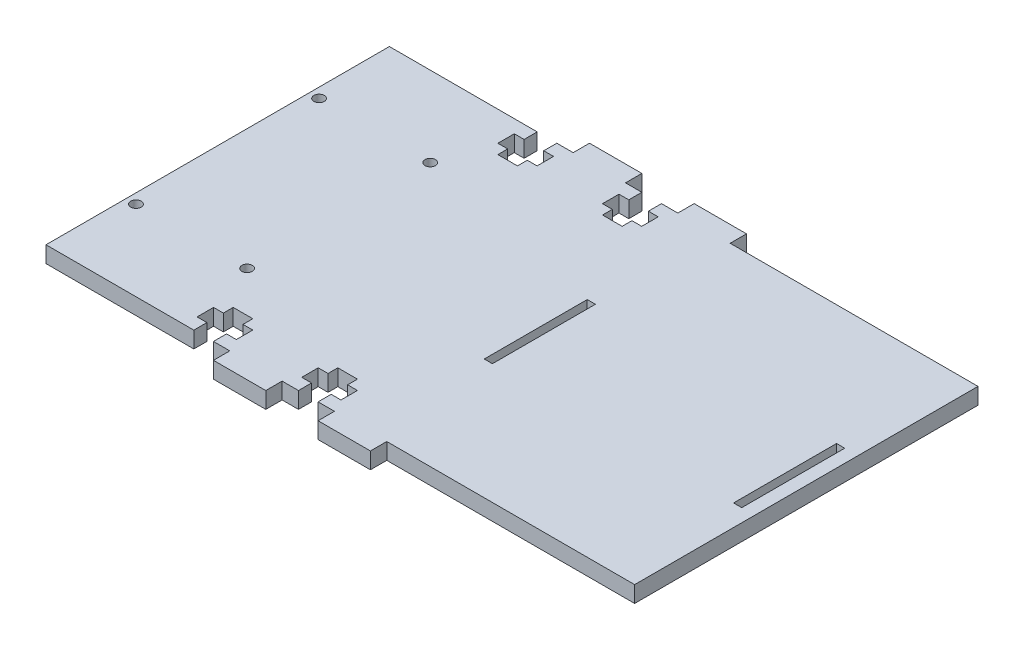
SolidWorks part; units mm, degrees
ref_plane "Front Plane" through (0, 0, 0) normal (0, 0, 1) x (1, 0, 0)
ref_plane "Top Plane" through (0, 0, 0) normal (0, 1, 0) x (1, 0, 0)
ref_plane "Right Plane" through (0, 0, 0) normal (1, 0, 0) x (0, 0, -1)
sketch "Sketch1" plane through (0, 0, 0) normal (0, 1, 0) x (1, 0, 0)
  line L1 (0, 0) -> (114.3, 0)
  line L2 (0, 0) -> (0, 66.675)
  line L3 (0, 66.675) -> (114.3, 66.675)
  line L4 (114.3, 0) -> (114.3, 66.675)
  line L8 (111.76, 43.3375) -> (110.1725, 43.3375)
  line L9 (111.76, 23.3375) -> (111.76, 43.3375)
  line L10 (110.1725, 23.3375) -> (111.76, 23.3375)
  line L11 (110.1725, 43.3375) -> (110.1725, 23.3375)
  line L12 (111.76, 43.3375) -> (110.1725, 43.3375)
  line L13 (111.76, 23.3375) -> (111.76, 43.3375)
  line L14 (110.1725, 23.3375) -> (111.76, 23.3375)
  line L15 (110.1725, 43.3375) -> (110.1725, 23.3375)
  line L16 (61.7601, 43.3375) -> (61.7601, 23.3375)
  line L17 (63.3476, 43.3375) -> (61.7601, 43.3375)
  line L18 (63.3476, 23.3375) -> (63.3476, 43.3375)
  line L19 (61.7601, 23.3375) -> (63.3476, 23.3375)
  line L20 (61.7601, 43.3375) -> (61.7601, 23.3375)
  line L21 (63.3476, 43.3375) -> (61.7601, 43.3375)
  line L22 (63.3476, 23.3375) -> (63.3476, 43.3375)
  line L23 (61.7601, 23.3375) -> (63.3476, 23.3375)
  circle A0 centre (1.905, 15.5575) radius 1.016 construction
  circle A1 centre (1.905, 15.5575) radius 1.016
  circle A2 centre (23.495, 15.5575) radius 1.016 construction
  circle A3 centre (23.495, 15.5575) radius 1.016
  circle A4 centre (23.495, 51.1175) radius 1.016 construction
  circle A5 centre (23.495, 51.1175) radius 1.016
  circle A6 centre (1.905, 51.1175) radius 1.016 construction
  circle A7 centre (1.905, 51.1175) radius 1.016
  dimension "D1" = 114.3
  dimension "D2" = 66.675
  dimension "D3" = 0
  dimension "D4" = 0
extrude "Boss-Extrude1" add sketch "Sketch1" along normal blind 3.175
sketch "Sketch2" plane through (0, 0, 0) normal (0, 0, 1) x (1, 0, 0)
  line L0 (0, 0) -> (114.3, 0) construction
  line L1 (0, 0) -> (114.3, 0) construction
  line L2 (0, 3.175) -> (114.3, 3.175) construction
  line L3 (0, 3.175) -> (114.3, 3.175) construction
  line L5 (20.4506, 0) -> (25.5306, 0)
  line L6 (20.4506, 0) -> (20.4506, 3.175)
  line L7 (20.4506, 3.175) -> (25.5306, 3.175)
  line L8 (25.5306, 0) -> (25.5306, 3.175)
  line L9 (25.5306, 0) -> (35.6906, 0)
  line L10 (25.5306, 0) -> (25.5306, 3.175)
  line L11 (25.5306, 3.175) -> (35.6906, 3.175)
  line L12 (35.6906, 0) -> (35.6906, 3.175)
  line L13 (35.6906, 0) -> (45.8506, 0)
  line L14 (35.6906, 0) -> (35.6906, 3.175)
  line L15 (35.6906, 3.175) -> (45.8506, 3.175)
  line L16 (45.8506, 0) -> (45.8506, 3.175)
  line L17 (45.8506, 0) -> (56.0106, 0)
  line L18 (45.8506, 0) -> (45.8506, 3.175)
  line L19 (45.8506, 3.175) -> (56.0106, 3.175)
  line L20 (56.0106, 0) -> (56.0106, 3.175)
  line L21 (56.0106, 0) -> (66.1706, 0)
  line L22 (56.0106, 0) -> (56.0106, 3.175)
  line L23 (56.0106, 3.175) -> (66.1706, 3.175)
  line L24 (66.1706, 0) -> (66.1706, 3.175)
  line L25 (66.1706, 0) -> (71.2506, 0)
  line L26 (66.1706, 0) -> (66.1706, 3.175)
  line L27 (66.1706, 3.175) -> (71.2506, 3.175)
  line L28 (71.2506, 0) -> (71.2506, 3.175)
  spline S0 degree 3 poles (-1129.5783, -3730.3547) (647.9287, 189.466) (-50.4594, 141.863) (-3.4984, 6.4532) (7.281, 2.3978) (14.7453, 0.8555) (28.8559, -1.3539) (189.1873, 0.9116) (392.4551, 31.0952) (-1336.1275, 3736.7279) knots -1.441349 -1.441349 -1.441349 -1.441349 0.267337 0.357506 0.391567 0.432957 0.471434 0.602901 2.8248 2.8248 2.8248 2.8248 only from (26.376, 58.8794) to (123.0381, 24.1743) construction
  spline S1 degree 3 poles (26.376, 58.8794) (6.7149, 58.4234) (-13.5307, 35.3809) (-3.4984, 6.4532) (7.281, 2.3978) (14.7453, 0.8555) (28.8559, -1.3539) (66.8662, -0.8168) (104.5934, 1.094) (123.0381, 24.1743) knots 0 0 0 0 0.267337 0.357506 0.391567 0.432957 0.471434 0.602901 1 1 1 1 construction
  point P6 (20.4506, 0)
  line M8 (0, 0) -> (114.3, 0)
  line M10 (114.3, 3.175) -> (0, 3.175)
  dimension "D1" = 5.08
  dimension "D2" = 10.16
  dimension "D3" = 10.16
  dimension "D4" = 10.16
  dimension "D5" = 10.16
  dimension "D6" = 5.08
ref_plane "Plane1" through (0, 3.175, -33.3375) normal (0, 0, -1) x (-1, 0, 0)
extrude "Boss-Extrude3" add sketch "Sketch2" along normal blind 3.175 contours L16 L12 M8 M10 | L24 L20 M8 M10
mirror "Mirror2" about plane through (0, 3.175, -33.3375) normal (0, 0, -1) of "Boss-Extrude3"
sketch "Sketch4" plane through (0, 3.175, 0) normal (0, 1, 0) x (1, 0, 0)
  line L0 (30.6106, 0) -> (30.6106, 7.6403) construction
  line L1 (25.5306, 0) -> (35.6906, 0) construction
  line L2 (28.7056, 0) -> (28.7056, 2.54)
  line L3 (0, 0) -> (35.6906, 0) construction
  line L4 (28.7056, 2.54) -> (26.8006, 2.54)
  line L5 (26.8006, 2.54) -> (26.8006, 5.7353)
  line L6 (26.8006, 5.7353) -> (28.7056, 5.7353)
  line L7 (28.7056, 5.7353) -> (28.7056, 7.6403)
  line L8 (28.7056, 7.6403) -> (32.5156, 7.6403)
  line L9 (32.5156, 5.7353) -> (32.5156, 7.6403)
  line L10 (34.4206, 5.7353) -> (32.5156, 5.7353)
  line L11 (34.4206, 2.54) -> (34.4206, 5.7353)
  line L12 (32.5156, 2.54) -> (34.4206, 2.54)
  line L13 (32.5156, 0) -> (32.5156, 2.54)
  line L14 (40.7706, -3.175) -> (40.7706, 0) construction
  line L15 (45.8506, -3.175) -> (35.6906, -3.175) construction
  line L16 (50.9306, 0) -> (50.9306, 7.6403) construction
  line L17 (49.0256, 0) -> (49.0256, 2.54)
  line L18 (49.0256, 2.54) -> (47.1206, 2.54)
  line L19 (47.1206, 2.54) -> (47.1206, 5.7353)
  line L20 (47.1206, 5.7353) -> (49.0256, 5.7353)
  line L21 (49.0256, 5.7353) -> (49.0256, 7.6403)
  line L22 (52.8356, 7.6403) -> (49.0256, 7.6403)
  line L23 (52.8356, 5.7353) -> (52.8356, 7.6403)
  line L24 (54.7406, 5.7353) -> (52.8356, 5.7353)
  line L25 (54.7406, 2.54) -> (54.7406, 5.7353)
  line L26 (52.8356, 2.54) -> (54.7406, 2.54)
  line L27 (52.8356, 0) -> (52.8356, 2.54)
  line L28 (0, 33.3375) -> (32.5156, 33.3375) construction
  line L29 (0, 66.675) -> (0, 0) construction
  line L30 (50.9306, 66.675) -> (50.9306, 59.0347) construction
  line L31 (30.6106, 66.675) -> (30.6106, 59.0347) construction
  line L32 (52.8356, 66.675) -> (52.8356, 64.135)
  line L33 (52.8356, 64.135) -> (54.7406, 64.135)
  line L34 (54.7406, 64.135) -> (54.7406, 60.9397)
  line L35 (54.7406, 60.9397) -> (52.8356, 60.9397)
  line L36 (52.8356, 60.9397) -> (52.8356, 59.0347)
  line L37 (52.8356, 59.0347) -> (49.0256, 59.0347)
  line L38 (49.0256, 60.9397) -> (49.0256, 59.0347)
  line L39 (47.1206, 60.9397) -> (49.0256, 60.9397)
  line L40 (47.1206, 64.135) -> (47.1206, 60.9397)
  line L41 (49.0256, 64.135) -> (47.1206, 64.135)
  line L42 (49.0256, 66.675) -> (49.0256, 64.135)
  line L43 (32.5156, 66.675) -> (32.5156, 64.135)
  line L44 (32.5156, 64.135) -> (34.4206, 64.135)
  line L45 (34.4206, 64.135) -> (34.4206, 60.9397)
  line L46 (34.4206, 60.9397) -> (32.5156, 60.9397)
  line L47 (32.5156, 60.9397) -> (32.5156, 59.0347)
  line L48 (28.7056, 59.0347) -> (32.5156, 59.0347)
  line L49 (28.7056, 60.9397) -> (28.7056, 59.0347)
  line L50 (26.8006, 60.9397) -> (28.7056, 60.9397)
  line L51 (26.8006, 64.135) -> (26.8006, 60.9397)
  line L52 (28.7056, 64.135) -> (26.8006, 64.135)
  line L53 (28.7056, 66.675) -> (28.7056, 64.135)
  line L54 (28.7056, 0) -> (32.5156, 0)
  line L55 (49.0256, 0) -> (52.8356, 0)
  line L56 (28.7056, 66.675) -> (32.5156, 66.675)
  line L57 (49.0256, 66.675) -> (52.8356, 66.675)
  dimension "D1" = 3.1953
  dimension "D2" = 2.54
  dimension "D3" = 1.905
  dimension "D4" = 3.81
  dimension "D5" = 1.905
extrude "Cut-Extrude1" cut sketch "Sketch4" against normal blind 3.175
